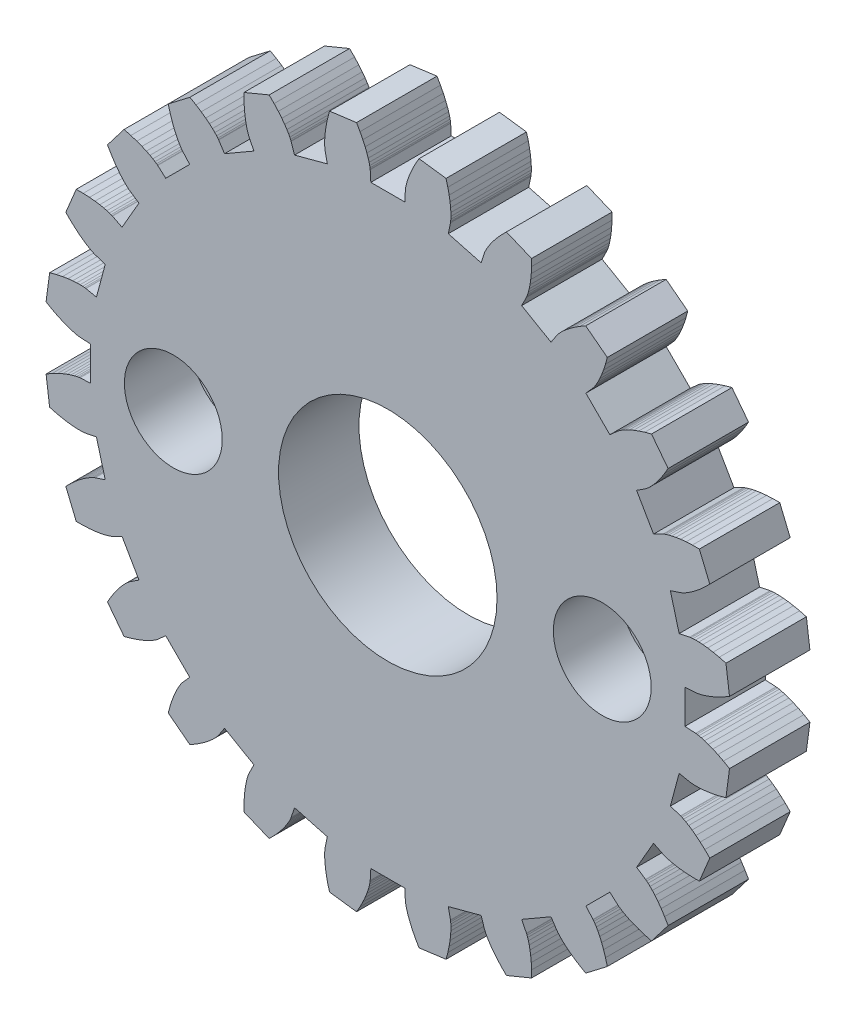
SolidWorks part; units mm, degrees
material "ABS"
ref_plane "Front Plane" through (0, 0, 0) normal (0, 0, 1) x (1, 0, 0)
ref_plane "Top Plane" through (0, 0, 0) normal (0, 1, 0) x (1, 0, 0)
ref_plane "Right Plane" through (0, 0, 0) normal (1, 0, 0) x (0, 0, -1)
sketch "Model" plane through (0, 0, 0) normal (0, 0, 1) x (1, 0, 0)
  line L0 (11.4813, -0.6559) -> (11.0819, -0.6331)
  line L1 (11.0819, -0.6331) -> (11.0819, 0.6331)
  line L2 (11.4813, 0.6559) -> (11.0819, 0.6331)
  line L3 (11.4813, 0.6559) -> (11.495, 0.6571)
  line L4 (11.495, 0.6571) -> (11.5358, 0.6626)
  line L5 (11.5358, 0.6626) -> (11.6033, 0.6749)
  line L6 (11.6033, 0.6749) -> (11.697, 0.6968)
  line L7 (11.697, 0.6968) -> (11.8158, 0.7307)
  line L8 (11.8158, 0.7307) -> (11.9589, 0.7792)
  line L9 (11.9589, 0.7792) -> (12.125, 0.8446)
  line L10 (12.125, 0.8446) -> (12.3128, 0.9294)
  line L11 (12.3128, 0.9294) -> (12.5206, 1.0358)
  line L12 (12.5206, 1.0358) -> (12.7468, 1.1658)
  line L13 (11.2598, 2.338) -> (11.2734, 2.3404)
  line L14 (11.2734, 2.3404) -> (11.3142, 2.3457)
  line L15 (11.3142, 2.3457) -> (11.3827, 2.3512)
  line L16 (11.3827, 2.3512) -> (11.4787, 2.3543)
  line L17 (11.4787, 2.3543) -> (11.6023, 2.3524)
  line L18 (11.6023, 2.3524) -> (11.7531, 2.3426)
  line L19 (11.7531, 2.3426) -> (11.9305, 2.3223)
  line L20 (11.9305, 2.3223) -> (12.1338, 2.289)
  line L21 (12.1338, 2.289) -> (12.362, 2.2401)
  line L22 (12.362, 2.2401) -> (12.6142, 2.173)
  line L23 (12.7468, 1.1658) -> (12.6142, 2.173)
  line L24 (11.2598, 2.338) -> (10.8682, 2.2567)
  line L25 (10.8682, 2.2567) -> (10.5405, 3.4797)
  line L26 (10.9203, 3.6051) -> (10.5405, 3.4797)
  line L27 (10.9203, 3.6051) -> (10.9332, 3.6098)
  line L28 (10.9332, 3.6098) -> (10.9712, 3.6257)
  line L29 (10.9712, 3.6257) -> (11.0333, 3.6551)
  line L30 (11.0333, 3.6551) -> (11.1181, 3.7004)
  line L31 (11.1181, 3.7004) -> (11.2241, 3.764)
  line L32 (11.2241, 3.764) -> (11.3497, 3.8478)
  line L33 (11.3497, 3.8478) -> (11.4933, 3.954)
  line L34 (11.4933, 3.954) -> (11.6527, 4.0845)
  line L35 (11.6527, 4.0845) -> (11.8259, 4.241)
  line L36 (11.8259, 4.241) -> (12.0107, 4.4252)
  line L37 (10.271, 5.1726) -> (10.2835, 5.1784)
  line L38 (10.2835, 5.1784) -> (10.3216, 5.1941)
  line L39 (10.3216, 5.1941) -> (10.3863, 5.2172)
  line L40 (10.3863, 5.2172) -> (10.4783, 5.245)
  line L41 (10.4783, 5.245) -> (10.5981, 5.2751)
  line L42 (10.5981, 5.2751) -> (10.7463, 5.3047)
  line L43 (10.7463, 5.3047) -> (10.9229, 5.331)
  line L44 (10.9229, 5.331) -> (11.1279, 5.3515)
  line L45 (11.1279, 5.3515) -> (11.361, 5.3633)
  line L46 (11.361, 5.3633) -> (11.622, 5.3638)
  line L47 (12.0107, 4.4252) -> (11.622, 5.3638)
  line L48 (10.271, 5.1726) -> (9.9138, 4.9927)
  line L49 (9.9138, 4.9927) -> (9.2807, 6.0892)
  line L50 (9.6151, 6.3087) -> (9.2807, 6.0892)
  line L51 (9.6151, 6.3087) -> (9.6264, 6.3166)
  line L52 (9.6264, 6.3166) -> (9.659, 6.3417)
  line L53 (9.659, 6.3417) -> (9.7113, 6.3862)
  line L54 (9.7113, 6.3862) -> (9.7815, 6.4519)
  line L55 (9.7815, 6.4519) -> (9.8675, 6.5407)
  line L56 (9.8675, 6.5407) -> (9.9671, 6.6542)
  line L57 (9.9671, 6.6542) -> (10.0783, 6.794)
  line L58 (10.0783, 6.794) -> (10.1985, 6.9613)
  line L59 (10.1985, 6.9613) -> (10.3253, 7.1573)
  line L60 (10.3253, 7.1573) -> (10.4561, 7.383)
  line L61 (8.5823, 7.6547) -> (8.5928, 7.6635)
  line L62 (8.5928, 7.6635) -> (8.6256, 7.6885)
  line L63 (8.6256, 7.6885) -> (8.6821, 7.7275)
  line L64 (8.6821, 7.7275) -> (8.7637, 7.7783)
  line L65 (8.7637, 7.7783) -> (8.8717, 7.8384)
  line L66 (8.8717, 7.8384) -> (9.0072, 7.9053)
  line L67 (9.0072, 7.9053) -> (9.1709, 7.9764)
  line L68 (9.1709, 7.9764) -> (9.3636, 8.0492)
  line L69 (9.3636, 8.0492) -> (9.5858, 8.121)
  line L70 (9.5858, 8.121) -> (9.8377, 8.189)
  line L71 (10.4561, 7.383) -> (9.8377, 8.189)
  line L72 (8.5823, 7.6547) -> (8.2838, 7.3885)
  line L73 (8.2838, 7.3885) -> (7.3885, 8.2838)
  line L74 (7.6547, 8.5823) -> (7.3885, 8.2838)
  line L75 (7.6547, 8.5823) -> (7.6635, 8.5928)
  line L76 (7.6635, 8.5928) -> (7.6885, 8.6256)
  line L77 (7.6885, 8.6256) -> (7.7275, 8.6821)
  line L78 (7.7275, 8.6821) -> (7.7783, 8.7637)
  line L79 (7.7783, 8.7637) -> (7.8384, 8.8717)
  line L80 (7.8384, 8.8717) -> (7.9053, 9.0072)
  line L81 (7.9053, 9.0072) -> (7.9764, 9.1709)
  line L82 (7.9764, 9.1709) -> (8.0492, 9.3636)
  line L83 (8.0492, 9.3636) -> (8.121, 9.5858)
  line L84 (8.121, 9.5858) -> (8.189, 9.8377)
  line L85 (6.3087, 9.6151) -> (6.3166, 9.6264)
  line L86 (6.3166, 9.6264) -> (6.3417, 9.659)
  line L87 (6.3417, 9.659) -> (6.3862, 9.7113)
  line L88 (6.3862, 9.7113) -> (6.4519, 9.7815)
  line L89 (6.4519, 9.7815) -> (6.5407, 9.8675)
  line L90 (6.5407, 9.8675) -> (6.6542, 9.9671)
  line L91 (6.6542, 9.9671) -> (6.794, 10.0783)
  line L92 (6.794, 10.0783) -> (6.9613, 10.1985)
  line L93 (6.9613, 10.1985) -> (7.1573, 10.3253)
  line L94 (7.1573, 10.3253) -> (7.383, 10.4561)
  line L95 (8.189, 9.8377) -> (7.383, 10.4561)
  line L96 (6.3087, 9.6151) -> (6.0892, 9.2807)
  line L97 (6.0892, 9.2807) -> (4.9927, 9.9138)
  line L98 (5.1726, 10.271) -> (4.9927, 9.9138)
  line L99 (5.1726, 10.271) -> (5.1784, 10.2835)
  line L100 (5.1784, 10.2835) -> (5.1941, 10.3216)
  line L101 (5.1941, 10.3216) -> (5.2172, 10.3863)
  line L102 (5.2172, 10.3863) -> (5.245, 10.4783)
  line L103 (5.245, 10.4783) -> (5.2751, 10.5981)
  line L104 (5.2751, 10.5981) -> (5.3047, 10.7463)
  line L105 (5.3047, 10.7463) -> (5.331, 10.9229)
  line L106 (5.331, 10.9229) -> (5.3515, 11.1279)
  line L107 (5.3515, 11.1279) -> (5.3633, 11.361)
  line L108 (5.3633, 11.361) -> (5.3638, 11.622)
  line L109 (3.6051, 10.9203) -> (3.6098, 10.9332)
  line L110 (3.6098, 10.9332) -> (3.6257, 10.9712)
  line L111 (3.6257, 10.9712) -> (3.6551, 11.0333)
  line L112 (3.6551, 11.0333) -> (3.7004, 11.1181)
  line L113 (3.7004, 11.1181) -> (3.764, 11.2241)
  line L114 (3.764, 11.2241) -> (3.8478, 11.3497)
  line L115 (3.8478, 11.3497) -> (3.954, 11.4933)
  line L116 (3.954, 11.4933) -> (4.0845, 11.6527)
  line L117 (4.0845, 11.6527) -> (4.241, 11.8259)
  line L118 (4.241, 11.8259) -> (4.4252, 12.0107)
  line L119 (5.3638, 11.622) -> (4.4252, 12.0107)
  line L120 (3.6051, 10.9203) -> (3.4797, 10.5405)
  line L121 (3.4797, 10.5405) -> (2.2567, 10.8682)
  line L122 (2.338, 11.2598) -> (2.2567, 10.8682)
  line L123 (2.338, 11.2598) -> (2.3404, 11.2734)
  line L124 (2.3404, 11.2734) -> (2.3457, 11.3142)
  line L125 (2.3457, 11.3142) -> (2.3512, 11.3827)
  line L126 (2.3512, 11.3827) -> (2.3543, 11.4787)
  line L127 (2.3543, 11.4787) -> (2.3524, 11.6023)
  line L128 (2.3524, 11.6023) -> (2.3426, 11.7531)
  line L129 (2.3426, 11.7531) -> (2.3223, 11.9305)
  line L130 (2.3223, 11.9305) -> (2.289, 12.1338)
  line L131 (2.289, 12.1338) -> (2.2401, 12.362)
  line L132 (2.2401, 12.362) -> (2.173, 12.6142)
  line L133 (0.6559, 11.4813) -> (0.6571, 11.495)
  line L134 (0.6571, 11.495) -> (0.6626, 11.5358)
  line L135 (0.6626, 11.5358) -> (0.6749, 11.6033)
  line L136 (0.6749, 11.6033) -> (0.6968, 11.697)
  line L137 (0.6968, 11.697) -> (0.7307, 11.8158)
  line L138 (0.7307, 11.8158) -> (0.7792, 11.9589)
  line L139 (0.7792, 11.9589) -> (0.8446, 12.125)
  line L140 (0.8446, 12.125) -> (0.9294, 12.3128)
  line L141 (0.9294, 12.3128) -> (1.0358, 12.5206)
  line L142 (1.0358, 12.5206) -> (1.1658, 12.7468)
  line L143 (2.173, 12.6142) -> (1.1658, 12.7468)
  line L144 (0.6559, 11.4813) -> (0.6331, 11.0819)
  line L145 (0.6331, 11.0819) -> (-0.6331, 11.0819)
  line L146 (-0.6559, 11.4813) -> (-0.6331, 11.0819)
  line L147 (-0.6559, 11.4813) -> (-0.6571, 11.495)
  line L148 (-0.6571, 11.495) -> (-0.6626, 11.5358)
  line L149 (-0.6626, 11.5358) -> (-0.6749, 11.6033)
  line L150 (-0.6749, 11.6033) -> (-0.6968, 11.697)
  line L151 (-0.6968, 11.697) -> (-0.7307, 11.8158)
  line L152 (-0.7307, 11.8158) -> (-0.7792, 11.9589)
  line L153 (-0.7792, 11.9589) -> (-0.8446, 12.125)
  line L154 (-0.8446, 12.125) -> (-0.9294, 12.3128)
  line L155 (-0.9294, 12.3128) -> (-1.0358, 12.5206)
  line L156 (-1.0358, 12.5206) -> (-1.1658, 12.7468)
  line L157 (-2.338, 11.2598) -> (-2.3404, 11.2734)
  line L158 (-2.3404, 11.2734) -> (-2.3457, 11.3142)
  line L159 (-2.3457, 11.3142) -> (-2.3512, 11.3827)
  line L160 (-2.3512, 11.3827) -> (-2.3543, 11.4787)
  line L161 (-2.3543, 11.4787) -> (-2.3524, 11.6023)
  line L162 (-2.3524, 11.6023) -> (-2.3426, 11.7531)
  line L163 (-2.3426, 11.7531) -> (-2.3223, 11.9305)
  line L164 (-2.3223, 11.9305) -> (-2.289, 12.1338)
  line L165 (-2.289, 12.1338) -> (-2.2401, 12.362)
  line L166 (-2.2401, 12.362) -> (-2.173, 12.6142)
  line L167 (-1.1658, 12.7468) -> (-2.173, 12.6142)
  line L168 (-2.338, 11.2598) -> (-2.2567, 10.8682)
  line L169 (-2.2567, 10.8682) -> (-3.4797, 10.5405)
  line L170 (-3.6051, 10.9203) -> (-3.4797, 10.5405)
  line L171 (-3.6051, 10.9203) -> (-3.6098, 10.9332)
  line L172 (-3.6098, 10.9332) -> (-3.6257, 10.9712)
  line L173 (-3.6257, 10.9712) -> (-3.6551, 11.0333)
  line L174 (-3.6551, 11.0333) -> (-3.7004, 11.1181)
  line L175 (-3.7004, 11.1181) -> (-3.764, 11.2241)
  line L176 (-3.764, 11.2241) -> (-3.8478, 11.3497)
  line L177 (-3.8478, 11.3497) -> (-3.954, 11.4933)
  line L178 (-3.954, 11.4933) -> (-4.0845, 11.6527)
  line L179 (-4.0845, 11.6527) -> (-4.241, 11.8259)
  line L180 (-4.241, 11.8259) -> (-4.4252, 12.0107)
  line L181 (-5.1726, 10.271) -> (-5.1784, 10.2835)
  line L182 (-5.1784, 10.2835) -> (-5.1941, 10.3216)
  line L183 (-5.1941, 10.3216) -> (-5.2172, 10.3863)
  line L184 (-5.2172, 10.3863) -> (-5.245, 10.4783)
  line L185 (-5.245, 10.4783) -> (-5.2751, 10.5981)
  line L186 (-5.2751, 10.5981) -> (-5.3047, 10.7463)
  line L187 (-5.3047, 10.7463) -> (-5.331, 10.9229)
  line L188 (-5.331, 10.9229) -> (-5.3515, 11.1279)
  line L189 (-5.3515, 11.1279) -> (-5.3633, 11.361)
  line L190 (-5.3633, 11.361) -> (-5.3638, 11.622)
  line L191 (-4.4252, 12.0107) -> (-5.3638, 11.622)
  line L192 (-5.1726, 10.271) -> (-4.9927, 9.9138)
  line L193 (-4.9927, 9.9138) -> (-6.0892, 9.2807)
  line L194 (-6.3087, 9.6151) -> (-6.0892, 9.2807)
  line L195 (-6.3087, 9.6151) -> (-6.3166, 9.6264)
  line L196 (-6.3166, 9.6264) -> (-6.3417, 9.659)
  line L197 (-6.3417, 9.659) -> (-6.3862, 9.7113)
  line L198 (-6.3862, 9.7113) -> (-6.4519, 9.7815)
  line L199 (-6.4519, 9.7815) -> (-6.5407, 9.8675)
  line L200 (-6.5407, 9.8675) -> (-6.6542, 9.9671)
  line L201 (-6.6542, 9.9671) -> (-6.794, 10.0783)
  line L202 (-6.794, 10.0783) -> (-6.9613, 10.1985)
  line L203 (-6.9613, 10.1985) -> (-7.1573, 10.3253)
  line L204 (-7.1573, 10.3253) -> (-7.383, 10.4561)
  line L205 (-7.6547, 8.5823) -> (-7.6635, 8.5928)
  line L206 (-7.6635, 8.5928) -> (-7.6885, 8.6256)
  line L207 (-7.6885, 8.6256) -> (-7.7275, 8.6821)
  line L208 (-7.7275, 8.6821) -> (-7.7783, 8.7637)
  line L209 (-7.7783, 8.7637) -> (-7.8384, 8.8717)
  line L210 (-7.8384, 8.8717) -> (-7.9053, 9.0072)
  line L211 (-7.9053, 9.0072) -> (-7.9764, 9.1709)
  line L212 (-7.9764, 9.1709) -> (-8.0492, 9.3636)
  line L213 (-8.0492, 9.3636) -> (-8.121, 9.5858)
  line L214 (-8.121, 9.5858) -> (-8.189, 9.8377)
  line L215 (-7.383, 10.4561) -> (-8.189, 9.8377)
  line L216 (-7.6547, 8.5823) -> (-7.3885, 8.2838)
  line L217 (-7.3885, 8.2838) -> (-8.2838, 7.3885)
  line L218 (-8.5823, 7.6547) -> (-8.2838, 7.3885)
  line L219 (-8.5823, 7.6547) -> (-8.5928, 7.6635)
  line L220 (-8.5928, 7.6635) -> (-8.6256, 7.6885)
  line L221 (-8.6256, 7.6885) -> (-8.6821, 7.7275)
  line L222 (-8.6821, 7.7275) -> (-8.7637, 7.7783)
  line L223 (-8.7637, 7.7783) -> (-8.8717, 7.8384)
  line L224 (-8.8717, 7.8384) -> (-9.0072, 7.9053)
  line L225 (-9.0072, 7.9053) -> (-9.1709, 7.9764)
  line L226 (-9.1709, 7.9764) -> (-9.3636, 8.0492)
  line L227 (-9.3636, 8.0492) -> (-9.5858, 8.121)
  line L228 (-9.5858, 8.121) -> (-9.8377, 8.189)
  line L229 (-9.6151, 6.3087) -> (-9.6264, 6.3166)
  line L230 (-9.6264, 6.3166) -> (-9.659, 6.3417)
  line L231 (-9.659, 6.3417) -> (-9.7113, 6.3862)
  line L232 (-9.7113, 6.3862) -> (-9.7815, 6.4519)
  line L233 (-9.7815, 6.4519) -> (-9.8675, 6.5407)
  line L234 (-9.8675, 6.5407) -> (-9.9671, 6.6542)
  line L235 (-9.9671, 6.6542) -> (-10.0783, 6.794)
  line L236 (-10.0783, 6.794) -> (-10.1985, 6.9613)
  line L237 (-10.1985, 6.9613) -> (-10.3253, 7.1573)
  line L238 (-10.3253, 7.1573) -> (-10.4561, 7.383)
  line L239 (-9.8377, 8.189) -> (-10.4561, 7.383)
  line L240 (-9.6151, 6.3087) -> (-9.2807, 6.0892)
  line L241 (-9.2807, 6.0892) -> (-9.9138, 4.9927)
  line L242 (-10.271, 5.1726) -> (-9.9138, 4.9927)
  line L243 (-10.271, 5.1726) -> (-10.2835, 5.1784)
  line L244 (-10.2835, 5.1784) -> (-10.3216, 5.1941)
  line L245 (-10.3216, 5.1941) -> (-10.3863, 5.2172)
  line L246 (-10.3863, 5.2172) -> (-10.4783, 5.245)
  line L247 (-10.4783, 5.245) -> (-10.5981, 5.2751)
  line L248 (-10.5981, 5.2751) -> (-10.7463, 5.3047)
  line L249 (-10.7463, 5.3047) -> (-10.9229, 5.331)
  line L250 (-10.9229, 5.331) -> (-11.1279, 5.3515)
  line L251 (-11.1279, 5.3515) -> (-11.361, 5.3633)
  line L252 (-11.361, 5.3633) -> (-11.622, 5.3638)
  line L253 (-10.9203, 3.6051) -> (-10.9332, 3.6098)
  line L254 (-10.9332, 3.6098) -> (-10.9712, 3.6257)
  line L255 (-10.9712, 3.6257) -> (-11.0333, 3.6551)
  line L256 (-11.0333, 3.6551) -> (-11.1181, 3.7004)
  line L257 (-11.1181, 3.7004) -> (-11.2241, 3.764)
  line L258 (-11.2241, 3.764) -> (-11.3497, 3.8478)
  line L259 (-11.3497, 3.8478) -> (-11.4933, 3.954)
  line L260 (-11.4933, 3.954) -> (-11.6527, 4.0845)
  line L261 (-11.6527, 4.0845) -> (-11.8259, 4.241)
  line L262 (-11.8259, 4.241) -> (-12.0107, 4.4252)
  line L263 (-11.622, 5.3638) -> (-12.0107, 4.4252)
  line L264 (-10.9203, 3.6051) -> (-10.5405, 3.4797)
  line L265 (-10.5405, 3.4797) -> (-10.8682, 2.2567)
  line L266 (-11.2598, 2.338) -> (-10.8682, 2.2567)
  line L267 (-11.2598, 2.338) -> (-11.2734, 2.3404)
  line L268 (-11.2734, 2.3404) -> (-11.3142, 2.3457)
  line L269 (-11.3142, 2.3457) -> (-11.3827, 2.3512)
  line L270 (-11.3827, 2.3512) -> (-11.4787, 2.3543)
  line L271 (-11.4787, 2.3543) -> (-11.6023, 2.3524)
  line L272 (-11.6023, 2.3524) -> (-11.7531, 2.3426)
  line L273 (-11.7531, 2.3426) -> (-11.9305, 2.3223)
  line L274 (-11.9305, 2.3223) -> (-12.1338, 2.289)
  line L275 (-12.1338, 2.289) -> (-12.362, 2.2401)
  line L276 (-12.362, 2.2401) -> (-12.6142, 2.173)
  line L277 (-11.4813, 0.6559) -> (-11.495, 0.6571)
  line L278 (-11.495, 0.6571) -> (-11.5358, 0.6626)
  line L279 (-11.5358, 0.6626) -> (-11.6033, 0.6749)
  line L280 (-11.6033, 0.6749) -> (-11.697, 0.6968)
  line L281 (-11.697, 0.6968) -> (-11.8158, 0.7307)
  line L282 (-11.8158, 0.7307) -> (-11.9589, 0.7792)
  line L283 (-11.9589, 0.7792) -> (-12.125, 0.8446)
  line L284 (-12.125, 0.8446) -> (-12.3128, 0.9294)
  line L285 (-12.3128, 0.9294) -> (-12.5206, 1.0358)
  line L286 (-12.5206, 1.0358) -> (-12.7468, 1.1658)
  line L287 (-12.6142, 2.173) -> (-12.7468, 1.1658)
  line L288 (-11.4813, 0.6559) -> (-11.0819, 0.6331)
  line L289 (-11.0819, 0.6331) -> (-11.0819, -0.6331)
  line L290 (-11.4813, -0.6559) -> (-11.0819, -0.6331)
  line L291 (-11.4813, -0.6559) -> (-11.495, -0.6571)
  line L292 (-11.495, -0.6571) -> (-11.5358, -0.6626)
  line L293 (-11.5358, -0.6626) -> (-11.6033, -0.6749)
  line L294 (-11.6033, -0.6749) -> (-11.697, -0.6968)
  line L295 (-11.697, -0.6968) -> (-11.8158, -0.7307)
  line L296 (-11.8158, -0.7307) -> (-11.9589, -0.7792)
  line L297 (-11.9589, -0.7792) -> (-12.125, -0.8446)
  line L298 (-12.125, -0.8446) -> (-12.3128, -0.9294)
  line L299 (-12.3128, -0.9294) -> (-12.5206, -1.0358)
  line L300 (-12.5206, -1.0358) -> (-12.7468, -1.1658)
  line L301 (-11.2598, -2.338) -> (-11.2734, -2.3404)
  line L302 (-11.2734, -2.3404) -> (-11.3142, -2.3457)
  line L303 (-11.3142, -2.3457) -> (-11.3827, -2.3512)
  line L304 (-11.3827, -2.3512) -> (-11.4787, -2.3543)
  line L305 (-11.4787, -2.3543) -> (-11.6023, -2.3524)
  line L306 (-11.6023, -2.3524) -> (-11.7531, -2.3426)
  line L307 (-11.7531, -2.3426) -> (-11.9305, -2.3223)
  line L308 (-11.9305, -2.3223) -> (-12.1338, -2.289)
  line L309 (-12.1338, -2.289) -> (-12.362, -2.2401)
  line L310 (-12.362, -2.2401) -> (-12.6142, -2.173)
  line L311 (-12.7468, -1.1658) -> (-12.6142, -2.173)
  line L312 (-11.2598, -2.338) -> (-10.8682, -2.2567)
  line L313 (-10.8682, -2.2567) -> (-10.5405, -3.4797)
  line L314 (-10.9203, -3.6051) -> (-10.5405, -3.4797)
  line L315 (-10.9203, -3.6051) -> (-10.9332, -3.6098)
  line L316 (-10.9332, -3.6098) -> (-10.9712, -3.6257)
  line L317 (-10.9712, -3.6257) -> (-11.0333, -3.6551)
  line L318 (-11.0333, -3.6551) -> (-11.1181, -3.7004)
  line L319 (-11.1181, -3.7004) -> (-11.2241, -3.764)
  line L320 (-11.2241, -3.764) -> (-11.3497, -3.8478)
  line L321 (-11.3497, -3.8478) -> (-11.4933, -3.954)
  line L322 (-11.4933, -3.954) -> (-11.6527, -4.0845)
  line L323 (-11.6527, -4.0845) -> (-11.8259, -4.241)
  line L324 (-11.8259, -4.241) -> (-12.0107, -4.4252)
  line L325 (-10.271, -5.1726) -> (-10.2835, -5.1784)
  line L326 (-10.2835, -5.1784) -> (-10.3216, -5.1941)
  line L327 (-10.3216, -5.1941) -> (-10.3863, -5.2172)
  line L328 (-10.3863, -5.2172) -> (-10.4783, -5.245)
  line L329 (-10.4783, -5.245) -> (-10.5981, -5.2751)
  line L330 (-10.5981, -5.2751) -> (-10.7463, -5.3047)
  line L331 (-10.7463, -5.3047) -> (-10.9229, -5.331)
  line L332 (-10.9229, -5.331) -> (-11.1279, -5.3515)
  line L333 (-11.1279, -5.3515) -> (-11.361, -5.3633)
  line L334 (-11.361, -5.3633) -> (-11.622, -5.3638)
  line L335 (-12.0107, -4.4252) -> (-11.622, -5.3638)
  line L336 (-10.271, -5.1726) -> (-9.9138, -4.9927)
  line L337 (-9.9138, -4.9927) -> (-9.2807, -6.0892)
  line L338 (-9.6151, -6.3087) -> (-9.2807, -6.0892)
  line L339 (-9.6151, -6.3087) -> (-9.6264, -6.3166)
  line L340 (-9.6264, -6.3166) -> (-9.659, -6.3417)
  line L341 (-9.659, -6.3417) -> (-9.7113, -6.3862)
  line L342 (-9.7113, -6.3862) -> (-9.7815, -6.4519)
  line L343 (-9.7815, -6.4519) -> (-9.8675, -6.5407)
  line L344 (-9.8675, -6.5407) -> (-9.9671, -6.6542)
  line L345 (-9.9671, -6.6542) -> (-10.0783, -6.794)
  line L346 (-10.0783, -6.794) -> (-10.1985, -6.9613)
  line L347 (-10.1985, -6.9613) -> (-10.3253, -7.1573)
  line L348 (-10.3253, -7.1573) -> (-10.4561, -7.383)
  line L349 (-8.5823, -7.6547) -> (-8.5928, -7.6635)
  line L350 (-8.5928, -7.6635) -> (-8.6256, -7.6885)
  line L351 (-8.6256, -7.6885) -> (-8.6821, -7.7275)
  line L352 (-8.6821, -7.7275) -> (-8.7637, -7.7783)
  line L353 (-8.7637, -7.7783) -> (-8.8717, -7.8384)
  line L354 (-8.8717, -7.8384) -> (-9.0072, -7.9053)
  line L355 (-9.0072, -7.9053) -> (-9.1709, -7.9764)
  line L356 (-9.1709, -7.9764) -> (-9.3636, -8.0492)
  line L357 (-9.3636, -8.0492) -> (-9.5858, -8.121)
  line L358 (-9.5858, -8.121) -> (-9.8377, -8.189)
  line L359 (-10.4561, -7.383) -> (-9.8377, -8.189)
  line L360 (-8.5823, -7.6547) -> (-8.2838, -7.3885)
  line L361 (-8.2838, -7.3885) -> (-7.3885, -8.2838)
  line L362 (-7.6547, -8.5823) -> (-7.3885, -8.2838)
  line L363 (-7.6547, -8.5823) -> (-7.6635, -8.5928)
  line L364 (-7.6635, -8.5928) -> (-7.6885, -8.6256)
  line L365 (-7.6885, -8.6256) -> (-7.7275, -8.6821)
  line L366 (-7.7275, -8.6821) -> (-7.7783, -8.7637)
  line L367 (-7.7783, -8.7637) -> (-7.8384, -8.8717)
  line L368 (-7.8384, -8.8717) -> (-7.9053, -9.0072)
  line L369 (-7.9053, -9.0072) -> (-7.9764, -9.1709)
  line L370 (-7.9764, -9.1709) -> (-8.0492, -9.3636)
  line L371 (-8.0492, -9.3636) -> (-8.121, -9.5858)
  line L372 (-8.121, -9.5858) -> (-8.189, -9.8377)
  line L373 (-6.3087, -9.6151) -> (-6.3166, -9.6264)
  line L374 (-6.3166, -9.6264) -> (-6.3417, -9.659)
  line L375 (-6.3417, -9.659) -> (-6.3862, -9.7113)
  line L376 (-6.3862, -9.7113) -> (-6.4519, -9.7815)
  line L377 (-6.4519, -9.7815) -> (-6.5407, -9.8675)
  line L378 (-6.5407, -9.8675) -> (-6.6542, -9.9671)
  line L379 (-6.6542, -9.9671) -> (-6.794, -10.0783)
  line L380 (-6.794, -10.0783) -> (-6.9613, -10.1985)
  line L381 (-6.9613, -10.1985) -> (-7.1573, -10.3253)
  line L382 (-7.1573, -10.3253) -> (-7.383, -10.4561)
  line L383 (-8.189, -9.8377) -> (-7.383, -10.4561)
  line L384 (-6.3087, -9.6151) -> (-6.0892, -9.2807)
  line L385 (-6.0892, -9.2807) -> (-4.9927, -9.9138)
  line L386 (-5.1726, -10.271) -> (-4.9927, -9.9138)
  line L387 (-5.1726, -10.271) -> (-5.1784, -10.2835)
  line L388 (-5.1784, -10.2835) -> (-5.1941, -10.3216)
  line L389 (-5.1941, -10.3216) -> (-5.2172, -10.3863)
  line L390 (-5.2172, -10.3863) -> (-5.245, -10.4783)
  line L391 (-5.245, -10.4783) -> (-5.2751, -10.5981)
  line L392 (-5.2751, -10.5981) -> (-5.3047, -10.7463)
  line L393 (-5.3047, -10.7463) -> (-5.331, -10.9229)
  line L394 (-5.331, -10.9229) -> (-5.3515, -11.1279)
  line L395 (-5.3515, -11.1279) -> (-5.3633, -11.361)
  line L396 (-5.3633, -11.361) -> (-5.3638, -11.622)
  line L397 (-3.6051, -10.9203) -> (-3.6098, -10.9332)
  line L398 (-3.6098, -10.9332) -> (-3.6257, -10.9712)
  line L399 (-3.6257, -10.9712) -> (-3.6551, -11.0333)
  line L400 (-3.6551, -11.0333) -> (-3.7004, -11.1181)
  line L401 (-3.7004, -11.1181) -> (-3.764, -11.2241)
  line L402 (-3.764, -11.2241) -> (-3.8478, -11.3497)
  line L403 (-3.8478, -11.3497) -> (-3.954, -11.4933)
  line L404 (-3.954, -11.4933) -> (-4.0845, -11.6527)
  line L405 (-4.0845, -11.6527) -> (-4.241, -11.8259)
  line L406 (-4.241, -11.8259) -> (-4.4252, -12.0107)
  line L407 (-5.3638, -11.622) -> (-4.4252, -12.0107)
  line L408 (-3.6051, -10.9203) -> (-3.4797, -10.5405)
  line L409 (-3.4797, -10.5405) -> (-2.2567, -10.8682)
  line L410 (-2.338, -11.2598) -> (-2.2567, -10.8682)
  line L411 (-2.338, -11.2598) -> (-2.3404, -11.2734)
  line L412 (-2.3404, -11.2734) -> (-2.3457, -11.3142)
  line L413 (-2.3457, -11.3142) -> (-2.3512, -11.3827)
  line L414 (-2.3512, -11.3827) -> (-2.3543, -11.4787)
  line L415 (-2.3543, -11.4787) -> (-2.3524, -11.6023)
  line L416 (-2.3524, -11.6023) -> (-2.3426, -11.7531)
  line L417 (-2.3426, -11.7531) -> (-2.3223, -11.9305)
  line L418 (-2.3223, -11.9305) -> (-2.289, -12.1338)
  line L419 (-2.289, -12.1338) -> (-2.2401, -12.362)
  line L420 (-2.2401, -12.362) -> (-2.173, -12.6142)
  line L421 (-0.6559, -11.4813) -> (-0.6571, -11.495)
  line L422 (-0.6571, -11.495) -> (-0.6626, -11.5358)
  line L423 (-0.6626, -11.5358) -> (-0.6749, -11.6033)
  line L424 (-0.6749, -11.6033) -> (-0.6968, -11.697)
  line L425 (-0.6968, -11.697) -> (-0.7307, -11.8158)
  line L426 (-0.7307, -11.8158) -> (-0.7792, -11.9589)
  line L427 (-0.7792, -11.9589) -> (-0.8446, -12.125)
  line L428 (-0.8446, -12.125) -> (-0.9294, -12.3128)
  line L429 (-0.9294, -12.3128) -> (-1.0358, -12.5206)
  line L430 (-1.0358, -12.5206) -> (-1.1658, -12.7468)
  line L431 (-2.173, -12.6142) -> (-1.1658, -12.7468)
  line L432 (-0.6559, -11.4813) -> (-0.6331, -11.0819)
  line L433 (-0.6331, -11.0819) -> (0.6331, -11.0819)
  line L434 (0.6559, -11.4813) -> (0.6331, -11.0819)
  line L435 (0.6559, -11.4813) -> (0.6571, -11.495)
  line L436 (0.6571, -11.495) -> (0.6626, -11.5358)
  line L437 (0.6626, -11.5358) -> (0.6749, -11.6033)
  line L438 (0.6749, -11.6033) -> (0.6968, -11.697)
  line L439 (0.6968, -11.697) -> (0.7307, -11.8158)
  line L440 (0.7307, -11.8158) -> (0.7792, -11.9589)
  line L441 (0.7792, -11.9589) -> (0.8446, -12.125)
  line L442 (0.8446, -12.125) -> (0.9294, -12.3128)
  line L443 (0.9294, -12.3128) -> (1.0358, -12.5206)
  line L444 (1.0358, -12.5206) -> (1.1658, -12.7468)
  line L445 (2.338, -11.2598) -> (2.3404, -11.2734)
  line L446 (2.3404, -11.2734) -> (2.3457, -11.3142)
  line L447 (2.3457, -11.3142) -> (2.3512, -11.3827)
  line L448 (2.3512, -11.3827) -> (2.3543, -11.4787)
  line L449 (2.3543, -11.4787) -> (2.3524, -11.6023)
  line L450 (2.3524, -11.6023) -> (2.3426, -11.7531)
  line L451 (2.3426, -11.7531) -> (2.3223, -11.9305)
  line L452 (2.3223, -11.9305) -> (2.289, -12.1338)
  line L453 (2.289, -12.1338) -> (2.2401, -12.362)
  line L454 (2.2401, -12.362) -> (2.173, -12.6142)
  line L455 (1.1658, -12.7468) -> (2.173, -12.6142)
  line L456 (2.338, -11.2598) -> (2.2567, -10.8682)
  line L457 (2.2567, -10.8682) -> (3.4797, -10.5405)
  line L458 (3.6051, -10.9203) -> (3.4797, -10.5405)
  line L459 (3.6051, -10.9203) -> (3.6098, -10.9332)
  line L460 (3.6098, -10.9332) -> (3.6257, -10.9712)
  line L461 (3.6257, -10.9712) -> (3.6551, -11.0333)
  line L462 (3.6551, -11.0333) -> (3.7004, -11.1181)
  line L463 (3.7004, -11.1181) -> (3.764, -11.2241)
  line L464 (3.764, -11.2241) -> (3.8478, -11.3497)
  line L465 (3.8478, -11.3497) -> (3.954, -11.4933)
  line L466 (3.954, -11.4933) -> (4.0845, -11.6527)
  line L467 (4.0845, -11.6527) -> (4.241, -11.8259)
  line L468 (4.241, -11.8259) -> (4.4252, -12.0107)
  line L469 (5.1726, -10.271) -> (5.1784, -10.2835)
  line L470 (5.1784, -10.2835) -> (5.1941, -10.3216)
  line L471 (5.1941, -10.3216) -> (5.2172, -10.3863)
  line L472 (5.2172, -10.3863) -> (5.245, -10.4783)
  line L473 (5.245, -10.4783) -> (5.2751, -10.5981)
  line L474 (5.2751, -10.5981) -> (5.3047, -10.7463)
  line L475 (5.3047, -10.7463) -> (5.331, -10.9229)
  line L476 (5.331, -10.9229) -> (5.3515, -11.1279)
  line L477 (5.3515, -11.1279) -> (5.3633, -11.361)
  line L478 (5.3633, -11.361) -> (5.3638, -11.622)
  line L479 (4.4252, -12.0107) -> (5.3638, -11.622)
  line L480 (5.1726, -10.271) -> (4.9927, -9.9138)
  line L481 (4.9927, -9.9138) -> (6.0892, -9.2807)
  line L482 (6.3087, -9.6151) -> (6.0892, -9.2807)
  line L483 (6.3087, -9.6151) -> (6.3166, -9.6264)
  line L484 (6.3166, -9.6264) -> (6.3417, -9.659)
  line L485 (6.3417, -9.659) -> (6.3862, -9.7113)
  line L486 (6.3862, -9.7113) -> (6.4519, -9.7815)
  line L487 (6.4519, -9.7815) -> (6.5407, -9.8675)
  line L488 (6.5407, -9.8675) -> (6.6542, -9.9671)
  line L489 (6.6542, -9.9671) -> (6.794, -10.0783)
  line L490 (6.794, -10.0783) -> (6.9613, -10.1985)
  line L491 (6.9613, -10.1985) -> (7.1573, -10.3253)
  line L492 (7.1573, -10.3253) -> (7.383, -10.4561)
  line L493 (7.6547, -8.5823) -> (7.6635, -8.5928)
  line L494 (7.6635, -8.5928) -> (7.6885, -8.6256)
  line L495 (7.6885, -8.6256) -> (7.7275, -8.6821)
  line L496 (7.7275, -8.6821) -> (7.7783, -8.7637)
  line L497 (7.7783, -8.7637) -> (7.8384, -8.8717)
  line L498 (7.8384, -8.8717) -> (7.9053, -9.0072)
  line L499 (7.9053, -9.0072) -> (7.9764, -9.1709)
  line L500 (7.9764, -9.1709) -> (8.0492, -9.3636)
  line L501 (8.0492, -9.3636) -> (8.121, -9.5858)
  line L502 (8.121, -9.5858) -> (8.189, -9.8377)
  line L503 (7.383, -10.4561) -> (8.189, -9.8377)
  line L504 (7.6547, -8.5823) -> (7.3885, -8.2838)
  line L505 (7.3885, -8.2838) -> (8.2838, -7.3885)
  line L506 (8.5823, -7.6547) -> (8.2838, -7.3885)
  line L507 (8.5823, -7.6547) -> (8.5928, -7.6635)
  line L508 (8.5928, -7.6635) -> (8.6256, -7.6885)
  line L509 (8.6256, -7.6885) -> (8.6821, -7.7275)
  line L510 (8.6821, -7.7275) -> (8.7637, -7.7783)
  line L511 (8.7637, -7.7783) -> (8.8717, -7.8384)
  line L512 (8.8717, -7.8384) -> (9.0072, -7.9053)
  line L513 (9.0072, -7.9053) -> (9.1709, -7.9764)
  line L514 (9.1709, -7.9764) -> (9.3636, -8.0492)
  line L515 (9.3636, -8.0492) -> (9.5858, -8.121)
  line L516 (9.5858, -8.121) -> (9.8377, -8.189)
  line L517 (9.6151, -6.3087) -> (9.6264, -6.3166)
  line L518 (9.6264, -6.3166) -> (9.659, -6.3417)
  line L519 (9.659, -6.3417) -> (9.7113, -6.3862)
  line L520 (9.7113, -6.3862) -> (9.7815, -6.4519)
  line L521 (9.7815, -6.4519) -> (9.8675, -6.5407)
  line L522 (9.8675, -6.5407) -> (9.9671, -6.6542)
  line L523 (9.9671, -6.6542) -> (10.0783, -6.794)
  line L524 (10.0783, -6.794) -> (10.1985, -6.9613)
  line L525 (10.1985, -6.9613) -> (10.3253, -7.1573)
  line L526 (10.3253, -7.1573) -> (10.4561, -7.383)
  line L527 (9.8377, -8.189) -> (10.4561, -7.383)
  line L528 (9.6151, -6.3087) -> (9.2807, -6.0892)
  line L529 (9.2807, -6.0892) -> (9.9138, -4.9927)
  line L530 (10.271, -5.1726) -> (9.9138, -4.9927)
  line L531 (10.271, -5.1726) -> (10.2835, -5.1784)
  line L532 (10.2835, -5.1784) -> (10.3216, -5.1941)
  line L533 (10.3216, -5.1941) -> (10.3863, -5.2172)
  line L534 (10.3863, -5.2172) -> (10.4783, -5.245)
  line L535 (10.4783, -5.245) -> (10.5981, -5.2751)
  line L536 (10.5981, -5.2751) -> (10.7463, -5.3047)
  line L537 (10.7463, -5.3047) -> (10.9229, -5.331)
  line L538 (10.9229, -5.331) -> (11.1279, -5.3515)
  line L539 (11.1279, -5.3515) -> (11.361, -5.3633)
  line L540 (11.361, -5.3633) -> (11.622, -5.3638)
  line L541 (10.9203, -3.6051) -> (10.9332, -3.6098)
  line L542 (10.9332, -3.6098) -> (10.9712, -3.6257)
  line L543 (10.9712, -3.6257) -> (11.0333, -3.6551)
  line L544 (11.0333, -3.6551) -> (11.1181, -3.7004)
  line L545 (11.1181, -3.7004) -> (11.2241, -3.764)
  line L546 (11.2241, -3.764) -> (11.3497, -3.8478)
  line L547 (11.3497, -3.8478) -> (11.4933, -3.954)
  line L548 (11.4933, -3.954) -> (11.6527, -4.0845)
  line L549 (11.6527, -4.0845) -> (11.8259, -4.241)
  line L550 (11.8259, -4.241) -> (12.0107, -4.4252)
  line L551 (11.622, -5.3638) -> (12.0107, -4.4252)
  line L552 (10.9203, -3.6051) -> (10.5405, -3.4797)
  line L553 (10.5405, -3.4797) -> (10.8682, -2.2567)
  line L554 (11.2598, -2.338) -> (10.8682, -2.2567)
  line L555 (11.2598, -2.338) -> (11.2734, -2.3404)
  line L556 (11.2734, -2.3404) -> (11.3142, -2.3457)
  line L557 (11.3142, -2.3457) -> (11.3827, -2.3512)
  line L558 (11.3827, -2.3512) -> (11.4787, -2.3543)
  line L559 (11.4787, -2.3543) -> (11.6023, -2.3524)
  line L560 (11.6023, -2.3524) -> (11.7531, -2.3426)
  line L561 (11.7531, -2.3426) -> (11.9305, -2.3223)
  line L562 (11.9305, -2.3223) -> (12.1338, -2.289)
  line L563 (12.1338, -2.289) -> (12.362, -2.2401)
  line L564 (12.362, -2.2401) -> (12.6142, -2.173)
  line L565 (11.4813, -0.6559) -> (11.495, -0.6571)
  line L566 (11.495, -0.6571) -> (11.5358, -0.6626)
  line L567 (11.5358, -0.6626) -> (11.6033, -0.6749)
  line L568 (11.6033, -0.6749) -> (11.697, -0.6968)
  line L569 (11.697, -0.6968) -> (11.8158, -0.7307)
  line L570 (11.8158, -0.7307) -> (11.9589, -0.7792)
  line L571 (11.9589, -0.7792) -> (12.125, -0.8446)
  line L572 (12.125, -0.8446) -> (12.3128, -0.9294)
  line L573 (12.3128, -0.9294) -> (12.5206, -1.0358)
  line L574 (12.5206, -1.0358) -> (12.7468, -1.1658)
  line L575 (12.6142, -2.173) -> (12.7468, -1.1658)
extrude "Main Gear Body" add sketch "Model" along normal blind 3
sketch "Sketch1" plane through (0, 0, 3) normal (0, 0, 1) x (1, 0, 0)
  line L0 (-8, 0) -> (8, 0) construction
  circle A0 centre (0, 0) radius 4.075
  circle A1 centre (-8, 0) radius 1.15
  circle A2 centre (8, 0) radius 1.15
  dimension "D1" = 16
  dimension "D2" = 2.3
  dimension "D3" = 8.15
extrude "Servo Clearance" cut sketch "Sketch1" against normal through all
sketch "Sketch2" plane through (0, 0, 3) normal (0, 0, 1) x (1, 0, 0)
  circle A0 centre (8, 0) radius 1.825
  circle A1 centre (-8, 0) radius 1.825
  circle A3 centre (-8, 0) radius 1.15 construction
  circle A4 centre (8, 0) radius 1.15 construction
  dimension "D1" = 3.65
extrude "Bolt Head Clearance" cut sketch "Sketch2" against normal blind 2.5
ref_point "Point1"
